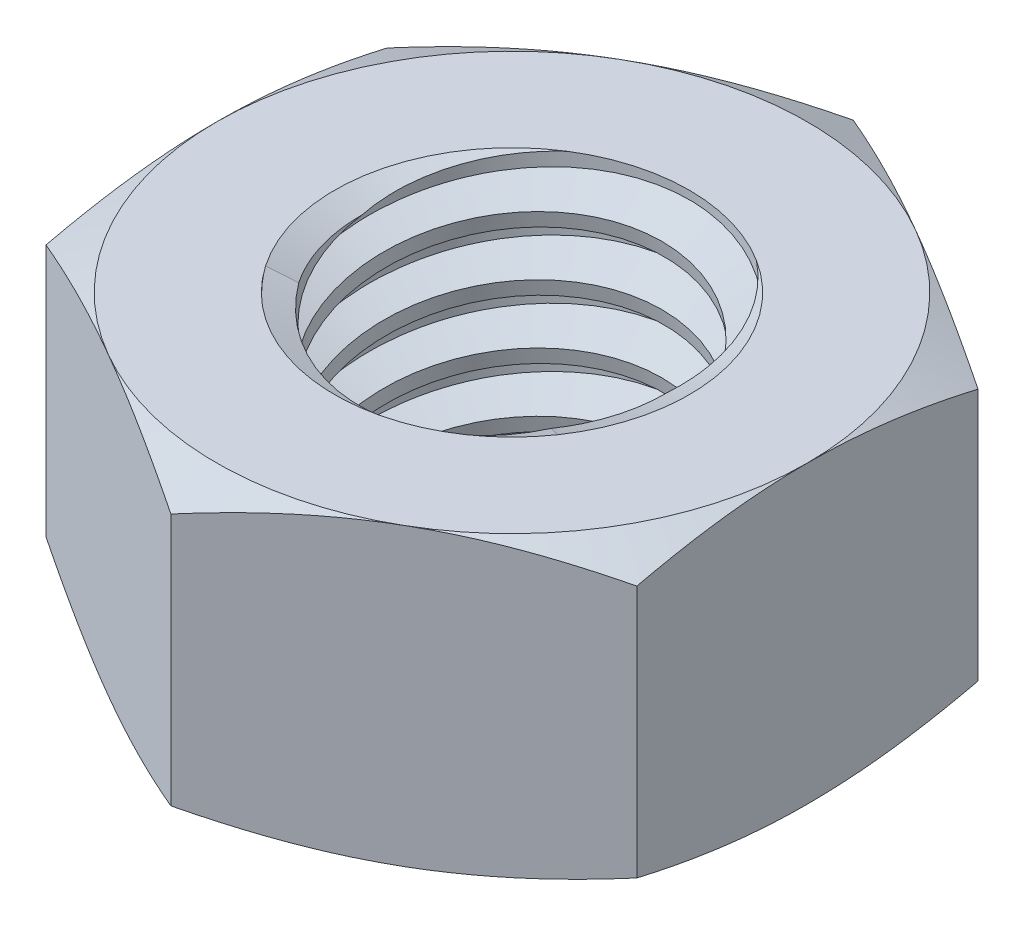
SolidWorks part; units mm, degrees
material "AISI 304"
ref_plane "Front" through (0, 0, 0) normal (0, 0, 1) x (1, 0, 0)
ref_plane "Top" through (0, 0, 0) normal (0, 1, 0) x (1, 0, 0)
ref_plane "Right" through (0, 0, 0) normal (1, 0, 0) x (0, 0, -1)
sketch "Sketch1" plane through (0, 0, 0) normal (0, 1, 0) x (1, 0, 0)
  line L1 (0, 5.7735) -> (-5, 2.8868)
  line L2 (-5, 2.8868) -> (-5, -2.8868)
  line L3 (-5, -2.8868) -> (0, -5.7735)
  line L4 (0, -5.7735) -> (5, -2.8868)
  line L5 (5, -2.8868) -> (5, 2.8868)
  line L6 (5, 2.8868) -> (0, 5.7735)
  circle A0 centre (0, 0) radius 5 construction
  dimension "Hex Flats" = 10
extrude "Extrude1" add sketch "Sketch1" along normal mid plane 5
sketch "Sketch2" plane through (0, 0, 0) normal (1, 0, 0) x (0, 0, -1)
  line L0 (-3, -2.5) -> (-3, 2.5) construction
  line L1 (0, -2.5) -> (3, -2.5)
  line L2 (0, -2.5) -> (0, 2.5)
  line L3 (0, 2.5) -> (3, 2.5)
  line L4 (3, -2.5) -> (3, 2.5)
  line L5 (-2.8868, 2.5) -> (2.8868, 2.5) construction
  line L6 (-2.8868, -2.5) -> (2.8868, -2.5) construction
  line L7 (0, -5.5) -> (0, -2.5) construction
  dimension "Thread Dia" = 6
revolve "Revolve1" add sketch "Sketch2" angle 360 about L7
sketch "Sketch3" plane through (0, 0, 0) normal (1, 0, 0) x (0, 0, -1)
  line L0 (3, 2.5) -> (-3, 2.5) construction
  line L1 (-3, 2.5) -> (-3, 1.5) construction
  line L2 (-3, 1.5) -> (3, 2.5) construction
  line L3 (3, 2.5) -> (3.0205, 2.3767) construction
  line L4 (3.0205, 2.3767) -> (3.1644, 1.5136)
  line L5 (3.1644, 1.5136) -> (2.5791, 1.7329)
  line L6 (2.5791, 1.7329) -> (2.538, 1.9795)
  line L7 (2.538, 1.9795) -> (3.0205, 2.3767)
  line L8 (2.5586, 1.8562) -> (3.0925, 1.9452) construction
  line L9 (3, 2.5) -> (3, 1.9297) construction
  line L10 (3, 1.9297) -> (-3, 0.9297) construction
  line L11 (-3, 0.9297) -> (-3, 1.5) construction
  line L12 (-0.1784, 2.5) -> (0.1784, 0.3595) construction
  line L13 (-3, -2.5) -> (-3, 2.5) construction
  line L14 (0, 2.5) -> (3, 2.5) construction
  line L15 (3, -2.5) -> (3, 2.5) construction
  line L16 (0, 0) -> (0, 2.5) construction
  line L17 (-3.0205, 2.3767) -> (-3.1644, 1.5136) construction
  line L18 (-2.538, 1.9795) -> (-3.0205, 2.3767) construction
  line L19 (-2.5791, 1.7329) -> (-2.538, 1.9795) construction
  line L20 (-3.1644, 1.5136) -> (-2.5791, 1.7329) construction
  line L21 (0.1784, 2.5) -> (-0.1784, 0.3595) construction
  point P13 (0, 1.4297)
  dimension "D1" = 0.125
  dimension "D2" = 0.25
  dimension "Thread Pitch" = 1
  dimension "D4" = 60
  dimension "D5" = 1
revolve "Cut-Revolve1" cut sketch "Sketch3" angle 360 about L12
pattern_linear "LPattern1" count 5 spacing 1 along (0, -1, 0) count 2 spacing 1 along (0, 1, 0) of "Cut-Revolve1"
sketch "Sketch4" plane through (0, 0, 0) normal (1, 0, 0) x (0, 0, -1)
  line L0 (0, 2.5) -> (3, 2.5)
  line L1 (3, 2.5) -> (2.538, 2.2846)
  line L2 (2.538, 2.2846) -> (2.538, -2.2846)
  line L3 (2.538, -2.2846) -> (3, -2.5)
  line L4 (3, -2.5) -> (0, -2.5)
  line L5 (0, -2.5) -> (0, 2.5)
  line L6 (3, -2.5) -> (3, 2.5) construction
  line L7 (0, 2.5) -> (3, 2.5) construction
  line L8 (0, -2.5) -> (3, -2.5) construction
  line L9 (0, -2.5) -> (0, 2.5) construction
  line L10 (0, 2.5) -> (0, 3.0097) construction
  dimension "D1" = 25
revolve "Cut-Revolve2" cut sketch "Sketch4" angle 360 about L10
combine bodies "Combine1" operation type subtract main body 112 bodies to subtract 111
sketch "Sketch5" plane through (0, 0, 0) normal (1, 0, 0) x (0, 0, -1)
  line L0 (0, -2.5) -> (5, -2.5)
  line L1 (5, -2.5) -> (5.7735, -2.1393)
  line L2 (5.7735, -2.1393) -> (5.7735, 2.1393)
  line L3 (5.7735, 2.1393) -> (5, 2.5)
  line L4 (0, 2.5) -> (0, 3.77)
  line L5 (0, 3.77) -> (7.0435, 3.77)
  line L6 (7.0435, 3.77) -> (7.0435, -3.77)
  line L7 (7.0435, -3.77) -> (0, -3.77)
  line L8 (0, -3.77) -> (0, -2.5)
  line L9 (5, 2.5) -> (5, -2.5) construction
  line L11 (0, -2.5) -> (3, -2.5) construction
  line L12 (5, 2.5) -> (0, 2.5)
  line L13 (5.7735, 0) -> (7.0435, 0) construction
  line L14 (5.7735, 2.5) -> (5.7735, -2.5) construction
  line L15 (0, -2.5) -> (0, 2.5) construction
  line L17 (0, 0) -> (5, 0) construction
  line L22 (0, 2.5) -> (3, 2.5) construction
  dimension "D1" = 25
  dimension "D2" = 1.27
  dimension "D3" = 5
revolve "Cut-Revolve3" cut sketch "Sketch5" angle 360 about L15
equation "\"D1@Sketch3\"=\"Thread Pitch@Sketch3\"/8"
equation "\"D2@Sketch3\"=\"Thread Pitch@Sketch3\"/4"
equation "\"D5@Sketch3\"=\"Thread Pitch@Sketch3\""
equation "\"D4@LPattern1\"=\"Thread Pitch@Sketch3\""
equation "\"D3@LPattern1\"=\"Thread Pitch@Sketch3\""
equation "\"D1@LPattern1\"=\"Height@Extrude1\"/\"Thread Pitch@Sketch3\""
